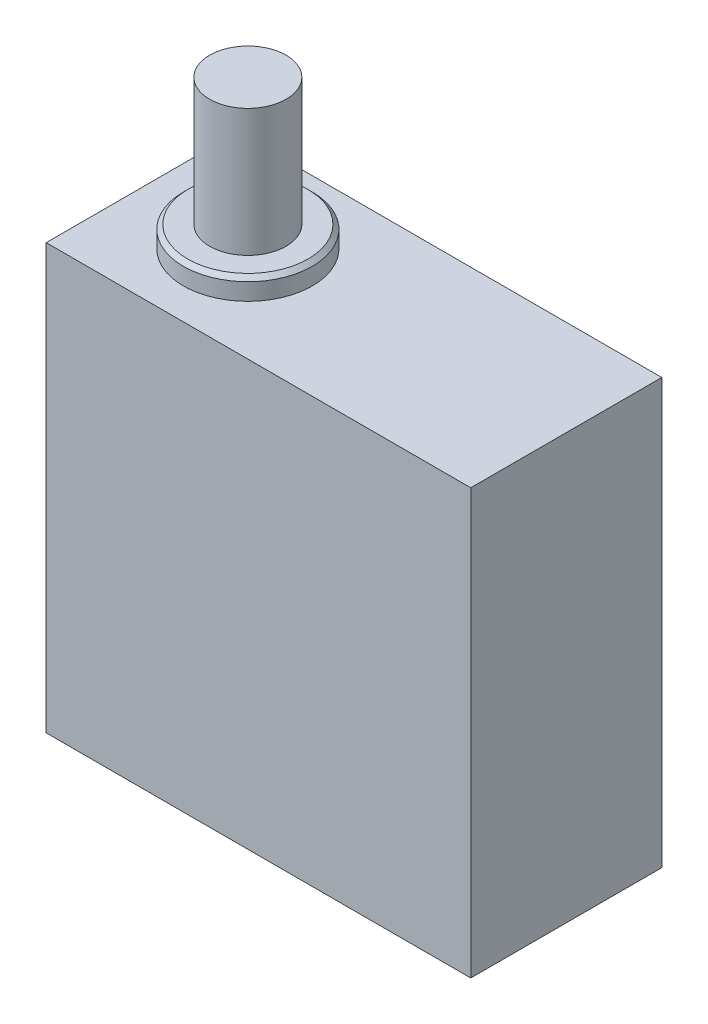
SolidWorks part; units mm, degrees
ref_plane "Face" through (0, 0, 0) normal (0, 0, 1) x (1, 0, 0)
ref_plane "Dessus" through (0, 0, 0) normal (0, 1, 0) x (1, 0, 0)
ref_plane "Droite" through (0, 0, 0) normal (1, 0, 0) x (0, 0, -1)
sketch "Esquisse1" plane through (0, 0, 0) normal (0, 0, 1) x (1, 0, 0)
  line L1 (0, 0) -> (20, 0)
  line L2 (0, 0) -> (0, 20)
  line L3 (0, 20) -> (20, 20)
  line L4 (20, 0) -> (20, 20)
  dimension "D1" = 20
extrude "Boss.-Extru.1" add sketch "Esquisse1" along normal blind 9
sketch "Esquisse2" plane through (0, 20, 0) normal (0, 1, 0) x (1, 0, 0)
  line L0 (0, 0) -> (10, -9)
  line L1 (20, -9) -> (0, -9) construction
  line L2 (0, -9) -> (10, 0)
  line L3 (20, 0) -> (0, 0) construction
  circle A0 centre (5, -4.5) radius 3.0352
extrude "Boss.-Extru.2" add sketch "Esquisse2" along normal blind 1 contours L2 A0 L0 | L0 A0 L2 | L0 A0 L2 | L2 A0 L0
chamfer "Chanfrein1" distance 0.2 angle 45 1 edges at (5, 21, 7.5352)
sketch "Esquisse4" plane through (0, 21, 0) normal (0, 1, 0) x (1, 0, 0)
  circle A0 centre (5, -4.5) radius 1.8
  dimension "D1" = 3.6
extrude "Boss.-Extru.3" add sketch "Esquisse4" along normal blind 6
